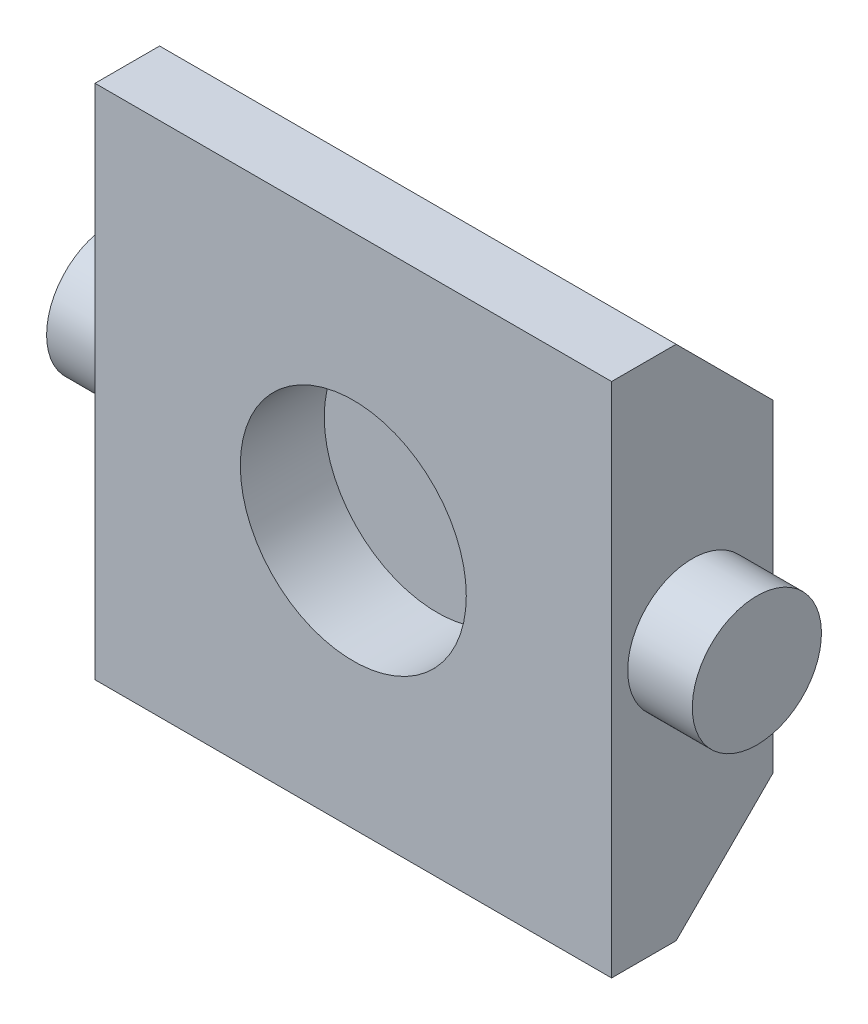
SolidWorks part; units mm, degrees
material "NITRONIC 60"
ref_plane "XY" through (0, 0, 0) normal (0, 0, 1) x (1, 0, 0)
ref_plane "XZ" through (0, 0, 0) normal (0, 1, 0) x (1, 0, 0)
ref_plane "YZ" through (0, 0, 0) normal (1, 0, 0) x (0, 0, -1)
sketch "Sketch1" plane through (0, 0, 0) normal (0, 0, 1) x (1, 0, 0)
  line L0 (25.4, 25.4) -> (-25.4, -25.4) construction
  line L1 (-25.4, 25.4) -> (25.4, 25.4)
  line L2 (-25.4, 25.4) -> (-25.4, -25.4)
  line L3 (-25.4, -25.4) -> (25.4, -25.4)
  line L4 (25.4, 25.4) -> (25.4, -25.4)
  dimension "D1" = 50.8
  dimension "D2" = 50.8
extrude "Extrude1" add sketch "Sketch1" along normal mid plane 15.875
sketch "Sketch6" plane through (0, 0, 7.9375) normal (0, 0, 1) x (1, 0, 0)
  circle A0 centre (0, 0) radius 11.1125
  dimension "D1" = 22.225
extrude "Cut-Extrude2" cut sketch "Sketch6" against normal blind 8.255
sketch "Sketch3" plane through (-25.4, 0, 0) normal (-1, 0, 0) x (0, 0, 1)
  line L0 (7.9375, 25.4) -> (7.9375, -25.4) construction
  circle A0 centre (0, 0) radius 6.35
  dimension "D1" = 12.7
  dimension "D2" = 7.9375
extrude "Extrude3" add sketch "Sketch3" along normal blind 6.35
mirror "Mirror2" about plane through (0, 0, 0) normal (1, 0, 0) of "Extrude3"
chamfer "Chamfer1" distance 9.525 angle 45 2 edges at (0, 25.4, -7.9375) (0, -25.4, -7.9375)
